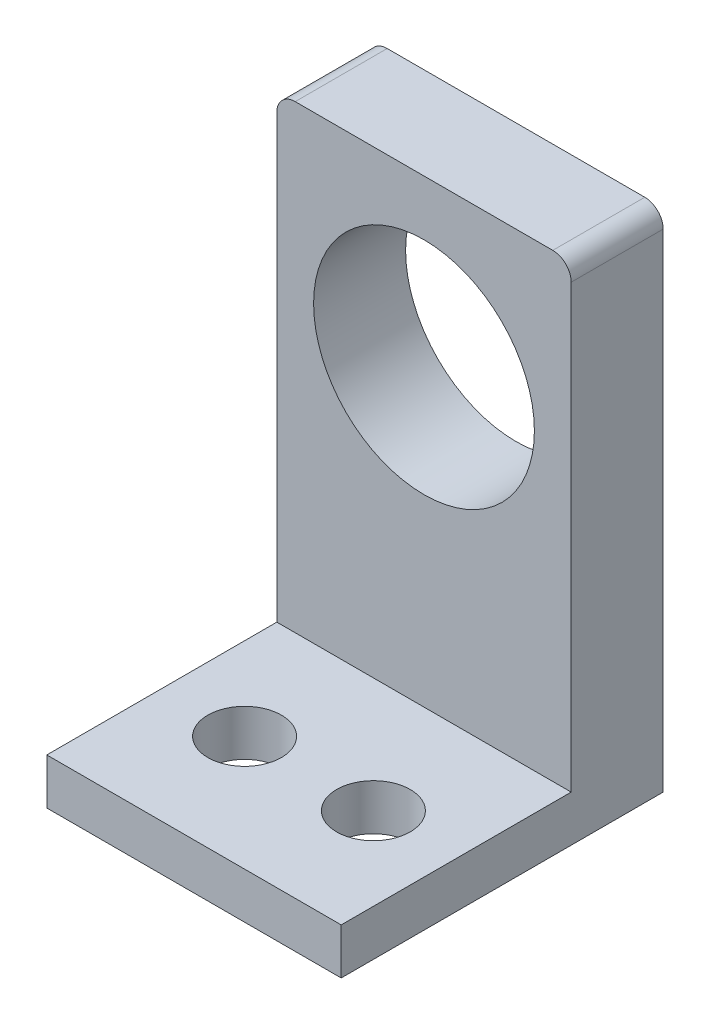
SolidWorks part; units mm, degrees
material "PET"
ref_plane "Front Plane" through (0, 0, 0) normal (0, 0, 1) x (1, 0, 0)
ref_plane "Top Plane" through (0, 0, 0) normal (0, 1, 0) x (1, 0, 0)
ref_plane "Right Plane" through (0, 0, 0) normal (1, 0, 0) x (0, 0, -1)
sketch "Sketch1" plane through (0, 0, 0) normal (0, 0, 1) x (1, 0, 0)
  line L1 (-16, -27.5) -> (16, -27.5)
  line L2 (-16, -27.5) -> (-16, 25.5)
  line L3 (-14, 27.5) -> (14, 27.5)
  line L4 (16, -27.5) -> (16, 25.5)
  line L5 (-16, -27.5) -> (16, 27.5) construction
  line L6 (-16, 27.5) -> (16, -27.5) construction
  circle A0 centre (0, 9.5) radius 12
  arc A1 (14, 27.5) -> (16, 25.5) centre (14, 25.5) cw
  arc A2 (-16, 25.5) -> (-14, 27.5) centre (-14, 25.5) cw
  point P0 (0, 0)
  dimension "D3" = 24
  dimension "D6" = 2
  dimension "D1" = 32
  dimension "D2" = 55
  dimension "D4" = 37
  dimension "D5" = 9.5
extrude "Boss-Extrude1" add sketch "Sketch1" along normal blind 10
sketch "Sketch2" plane through (0, 0, 10) normal (0, 0, 1) x (1, 0, 0)
  line L0 (16, -27.5) -> (16, 25.5) construction
  line L1 (-16, -27.5) -> (16, -27.5)
  line L2 (-16, -27.5) -> (-16, -22.5)
  line L3 (-16, -22.5) -> (16, -22.5)
  line L4 (16, -27.5) -> (16, -22.5)
  dimension "D1" = 5
extrude "Boss-Extrude2" add sketch "Sketch2" along normal blind 25
sketch "Sketch3" plane through (0, -22.5, 0) normal (0, 1, 0) x (1, 0, 0)
  line L0 (16, -35) -> (-16, -35) construction
  line L1 (-16, -35) -> (-16, -10) construction
  line L2 (16, -35) -> (16, -10) construction
  circle A0 centre (-7, -22.5) radius 4
  circle A1 centre (7, -22.5) radius 4
  point P10 (0, 0)
  point P12 (16, -23.0015)
  dimension "D1" = 8
  dimension "D2" = 8
  dimension "D3" = 12.5
  dimension "D4" = 9
  dimension "D5" = 9
  dimension "D6" = 12.5
extrude "Cut-Extrude1" cut sketch "Sketch3" against normal blind 25
